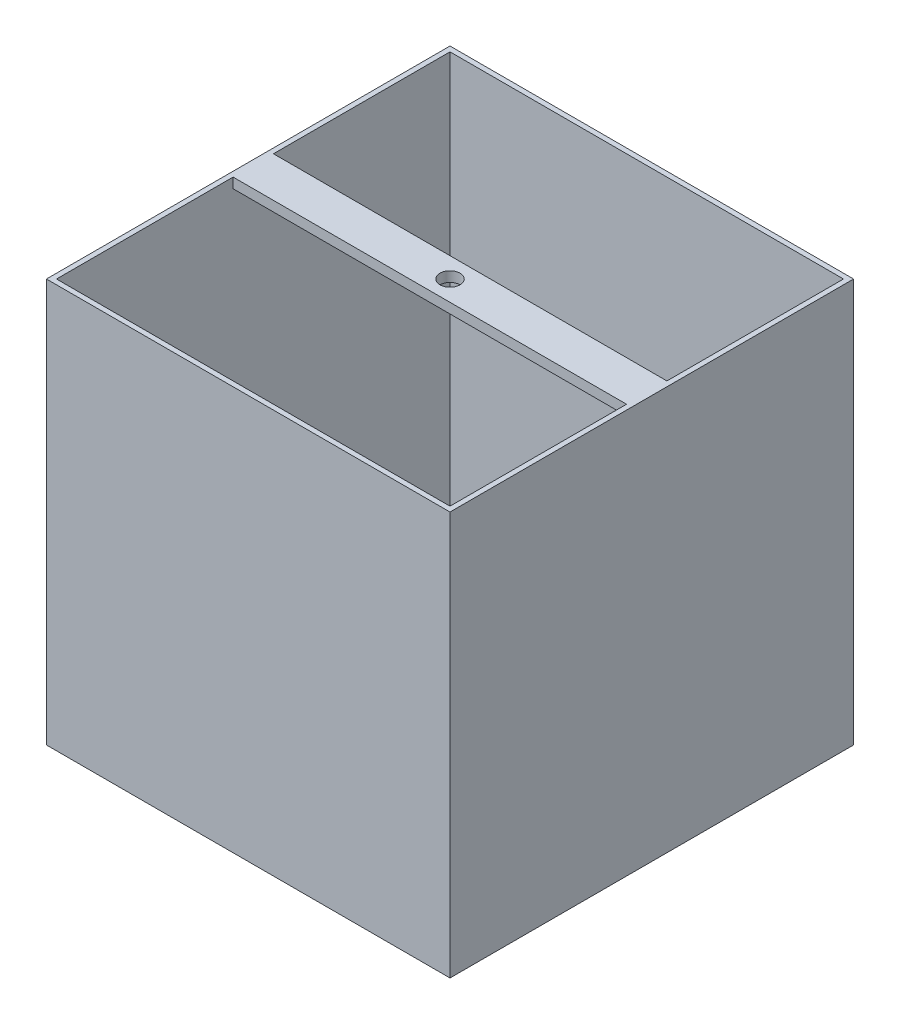
SolidWorks part; units mm, degrees
ref_plane "Front Plane" through (0, 0, 0) normal (0, 0, 1) x (1, 0, 0)
ref_plane "Top Plane" through (0, 0, 0) normal (0, 1, 0) x (1, 0, 0)
ref_plane "Right Plane" through (0, 0, 0) normal (1, 0, 0) x (0, 0, -1)
sketch "Sketch1" plane through (0, 0, 0) normal (0, 1, 0) x (1, 0, 0)
  line L1 (-127, 127) -> (127, 127)
  line L2 (-127, 127) -> (-127, -127)
  line L3 (-127, -127) -> (127, -127)
  line L4 (127, 127) -> (127, -127)
  line L5 (-127, 127) -> (127, -127) construction
  line L6 (-127, -127) -> (127, 127) construction
  point P0 (0, 0)
  dimension "D1" = 254
  dimension "D2" = 254
extrude "Boss-Extrude1" add sketch "Sketch1" along normal blind 254
sketch "Sketch2" plane through (0, 254, 0) normal (0, 1, 0) x (1, 0, 0)
  line L1 (-123.825, 123.825) -> (123.825, 123.825)
  line L2 (-123.825, 123.825) -> (-123.825, -123.825)
  line L3 (-123.825, -123.825) -> (123.825, -123.825)
  line L4 (123.825, 123.825) -> (123.825, -123.825)
  line L5 (-123.825, 123.825) -> (123.825, -123.825) construction
  line L6 (-123.825, -123.825) -> (123.825, 123.825) construction
  point P0 (0, 0)
  dimension "D1" = 247.65
  dimension "D2" = 247.65
extrude "Cut-Extrude1" cut sketch "Sketch2" against normal blind 247.65
sketch "Sketch3" plane through (0, 6.35, 0) normal (0, 1, 0) x (1, 0, 0)
  circle A0 centre (0, 0) radius 6.35
  dimension "D1" = 12.7
extrude "Cut-Extrude2" cut sketch "Sketch3" against normal blind 247.65
sketch "Sketch4" plane through (0, 254, 0) normal (0, 1, 0) x (1, 0, 0)
  line L5 (123.825, -123.825) -> (123.825, 123.825) construction
  line L6 (-123.825, 12.7) -> (123.825, 12.7)
  line L7 (-123.825, 12.7) -> (-123.825, -12.7)
  line L8 (-123.825, -12.7) -> (123.825, -12.7)
  line L9 (123.825, 12.7) -> (123.825, -12.7)
  line L10 (-123.825, 12.7) -> (123.825, -12.7) construction
  line L11 (-123.825, -12.7) -> (123.825, 12.7) construction
  circle A0 centre (0, 0) radius 6.35
  point P0 (0, 0)
  point P1 (0, 0)
  dimension "D2" = 12.7
  dimension "D1" = 25.4
extrude "Boss-Extrude2" add sketch "Sketch4" against normal blind 6.35
